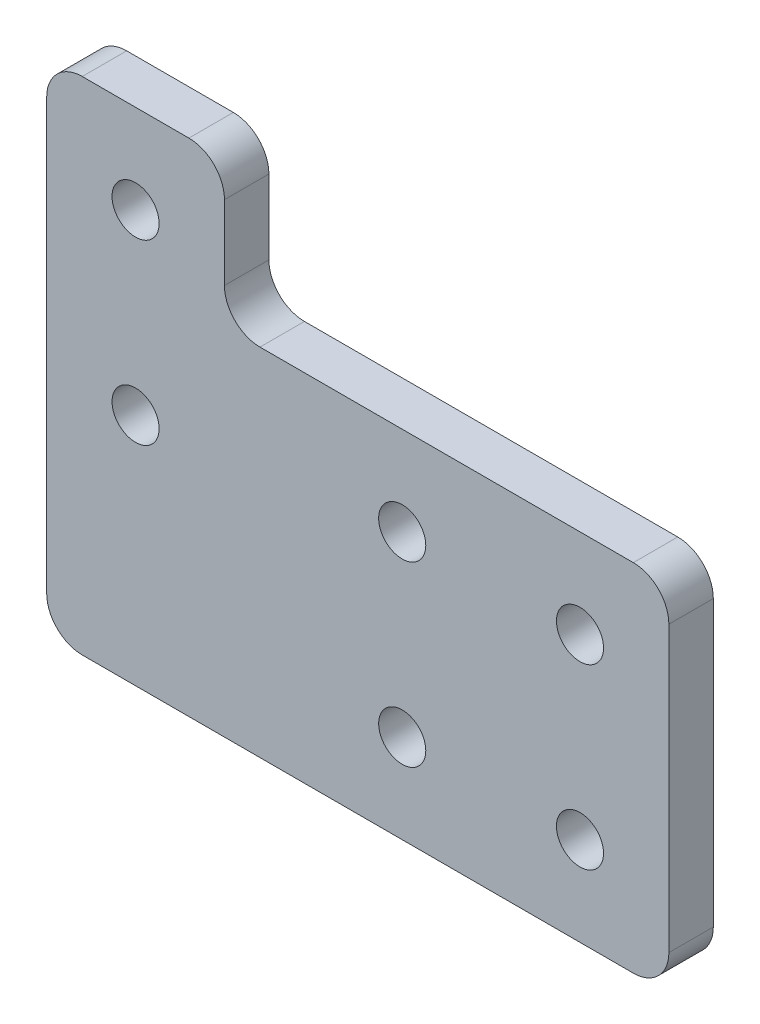
SolidWorks part; units mm, degrees
ref_plane "Front Face Plane" through (0, 0, 0) normal (0, 0, 1) x (1, 0, 0)
ref_plane "Top Plane" through (0, 0, 0) normal (0, 1, 0) x (1, 0, 0)
ref_plane "Right Plane" through (0, 0, 0) normal (1, 0, 0) x (0, 0, -1)
ref_plane "Back Face Plane" through (0, 0, 5) normal (0, 0, 1) x (1, 0, 0)
sketch "End Cap Sketch" plane through (0, 0, 0) normal (0, 0, 1) x (1, 0, 0)
  line L0 (-46, -20) -> (16, -20)
  line L1 (20, -16) -> (20, 16)
  line L2 (16, 20) -> (-26, 20)
  line L4 (-30, 24) -> (-30, 32.365)
  line L5 (-34, 36.365) -> (-46, 36.365)
  line L6 (-50, 32.365) -> (-50, -16)
  line L7 (20, 0) -> (-50, 0) construction
  circle A0 centre (-10, 10) radius 2.65
  circle A1 centre (-10, -10) radius 2.65
  circle A2 centre (10, 10) radius 2.65
  circle A3 centre (10, -10) radius 2.65
  circle A4 centre (-40, 26.365) radius 2.65
  circle A5 centre (-40, 6.365) radius 2.65
  arc A6 (-26, 20) -> (-30, 24) centre (-26, 24) cw
  arc A7 (-30, 32.365) -> (-34, 36.365) centre (-34, 32.365) ccw
  arc A8 (-46, 36.365) -> (-50, 32.365) centre (-46, 32.365) ccw
  arc A9 (-50, -16) -> (-46, -20) centre (-46, -16) ccw
  arc A10 (16, -20) -> (20, -16) centre (16, -16) ccw
  arc A11 (20, 16) -> (16, 20) centre (16, 16) ccw
  point P31 (-30, 36.365)
  point P37 (-50, 36.365)
  point P42 (20, -20)
  point P45 (20, 20)
  dimension "D2" = 5.3
  dimension "D7" = 50
  dimension "D12" = 10
  dimension "D19" = 4
  dimension "D1" = 40
  dimension "D3" = 10
  dimension "D4" = 10
  dimension "D5" = 10
  dimension "D6" = 10
  dimension "D8" = 20
  dimension "D9" = 20
  dimension "D10" = 20
  dimension "D11" = 10
  dimension "D18" = 6.365
extrude "Extrude Thickness" add sketch "End Cap Sketch" along normal blind 5
equation "\"Pulley Y Position\"= 38mm"
